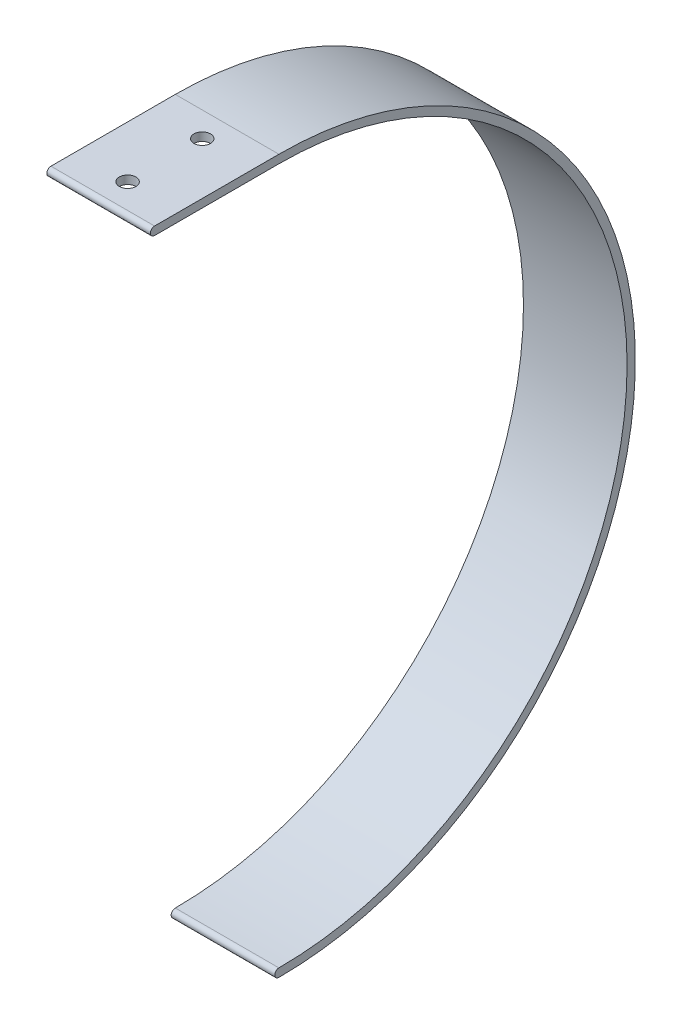
SolidWorks part; units mm, degrees
material "S-Glass Fiber"
ref_plane "Front Plane" through (0, 0, 0) normal (0, 0, 1) x (1, 0, 0)
ref_plane "Top Plane" through (0, 0, 0) normal (0, 1, 0) x (1, 0, 0)
ref_plane "Right Plane" through (0, 0, 0) normal (1, 0, 0) x (0, 0, -1)
sketch "Sketch1" plane through (0, 0, 0) normal (1, 0, 0) x (0, 0, -1)
  line L0 (10, 85) -> (10, -85) construction
  line L1 (10, 85) -> (-20, 85) construction
  line L2 (10, 84) -> (-20, 84)
  line L3 (10, 86) -> (-20, 86)
  arc A0 (10, 84) -> (10, -84) centre (10, 0) cw
  arc A1 (10, 85) -> (10, -85) centre (10, 0) cw construction
  arc A2 (10, 86) -> (10, -86) centre (10, 0) cw
  arc A3 (-20, 84) -> (-20, 86) centre (-20, 85) cw
  arc A4 (10, -84) -> (10, -86) centre (10, -85) ccw
  dimension "D1" = 1
  dimension "D3" = 1
  dimension "D4" = 85
  dimension "D2" = 30
extrude "Boss-Extrude1" add sketch "Sketch1" along normal blind 25
hole_wizard "Ø4.0mm Dowel Hole1" positions "Sketch3" profile "Sketch2" hole size "Ø4.0" standard "ISO"
sketch "Sketch3" plane through (0, 86, 0) normal (0, 1, 0) x (1, 0, 0)
  line L1 (25, 10) -> (0, 10) construction
  point P4 (12.5, -14)
  point P17 (12.5, 4)
  dimension "D1" = 18
  dimension "D2" = 6
sketch "Sketch2" plane through (12.5, 86, 14) normal (1, 0, 0) x (0, 0, 1)
  line L0 (0, 0) -> (0, 18.4917)
  line L1 (0, 18.4917) -> (2, 17.29)
  line L2 (2, 17.29) -> (2, 0)
  line L5 (2, 0) -> (0, 0)
  line L10 (0, 18.4917) -> (-2, 17.29) construction
  line L11 (0, -6.35) -> (0, 107.95) construction
  dimension "Hole Dia." = 4
  dimension "Hole Depth" = 17.29
  dimension "Drill Angle" = 118
